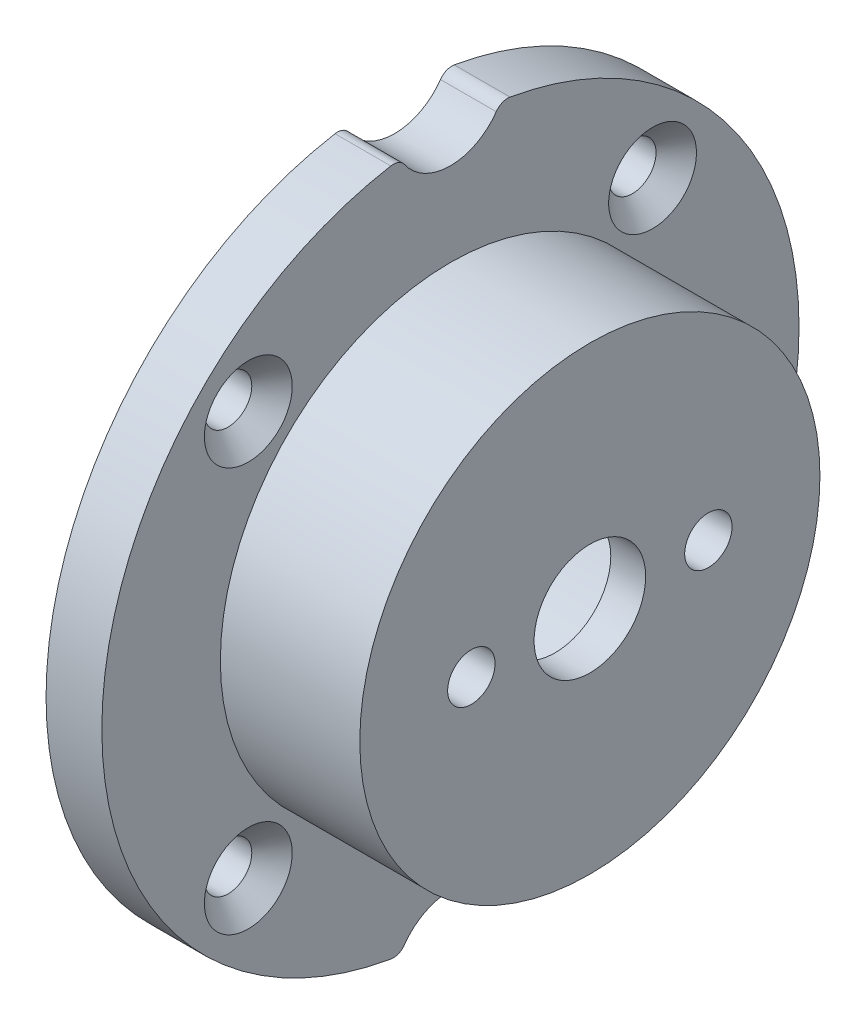
SolidWorks part; units mm, degrees
material "ABS"
ref_plane "Front Plane" through (0, 0, 0) normal (0, 0, 1) x (1, 0, 0)
ref_plane "Top Plane" through (0, 0, 0) normal (0, 1, 0) x (1, 0, 0)
ref_plane "Right Plane" through (0, 0, 0) normal (1, 0, 0) x (0, 0, -1)
sketch "Sketch1" plane through (0, 0, 0) normal (1, 0, 0) x (0, 0, -1)
  circle A0 centre (0, 0) radius 25
extrude "Boss-Extrude1" add sketch "Sketch1" along normal blind 4
sketch "Sketch2" plane through (4, 0, 0) normal (1, 0, 0) x (0, 0, -1)
  circle A0 centre (0, 0) radius 16.5
extrude "Boss-Extrude2" add sketch "Sketch2" along normal blind 10
sketch "Sketch3" plane through (0, 0, 0) normal (-1, 0, 0) x (0, 0, 1)
  circle A0 centre (0, 0) radius 12.5
extrude "Cut-Extrude1" cut sketch "Sketch3" against normal offset from surface (11.5 mm away) 2.5 up to face at (14, 0, -16.5)
sketch "Sketch4" plane through (14, 0, 0) normal (1, 0, 0) x (0, 0, -1)
  circle A0 centre (0, 0) radius 4
extrude "Cut-Extrude2" cut sketch "Sketch4" against normal blind 4
hole_wizard "M3 Clearance Hole1" positions "Sketch6" profile "Sketch5" hole size "M3" standard "ANSI Metric"
sketch "Sketch6" plane through (14, 0, 0) normal (1, 0, 0) x (0, 0, -1)
  point P0 (8.5, 0)
  point P2 (-8.5, 0)
  dimension "D1" = 8.5
  dimension "D2" = 8.5
sketch "Sketch5" plane through (14, 0, -8.5) normal (0, 1, 0) x (0, 0, -1)
  line L0 (0, 0) -> (0, 10)
  line L1 (0, 10) -> (1.7, 10)
  line L2 (1.7, 10) -> (1.7, 0)
  line L5 (1.7, 0) -> (0, 0)
  line L10 (0, 10) -> (-1.7, 10) construction
  line L11 (0, -6.35) -> (0, 107.95) construction
  dimension "Hole Dia." = 3.4
  dimension "Hole Depth" = 10
  dimension "Drill Angle" = 180
sketch "Sketch7" plane through (4, 0, 0) normal (1, 0, 0) x (0, 0, -1)
  line L0 (0, 0) -> (-14.4957, -14.4957) construction
hole_wizard "CSK for M3 Flat Head Machine Screw1" positions "Sketch9" profile "Sketch8" countersink size "M3" standard "ANSI Metric" end condition through all
sketch "Sketch9" plane through (4, 0, 0) normal (1, 0, 0) x (0, 0, -1)
  point P0 (-14.4957, -14.4957)
sketch "Sketch8" plane through (4, -14.4957, 14.4957) normal (0, 1, 0) x (0, 0, -1)
  line L0 (0, 0) -> (0, 4)
  line L1 (0, 4) -> (1.7, 4)
  line L2 (1.7, 4) -> (1.7, 1.45)
  line L3 (1.7, 1.45) -> (3.15, 0)
  line L5 (3.15, 0) -> (0, 0)
  line L6 (-1.7, 1.45) -> (-3.15, 0) construction
  line L11 (0, -6.35) -> (0, 107.95) construction
  dimension "Thru Hole Dia." = 3.4
  dimension "Thru Hole Depth" = 4
  dimension "Near C'Sink Dia." = 6.3
  dimension "Near C'Sink Angle" = 90
pattern_circular "CirPattern1" count 4 over 360 about axis through (0, 0, 0) along (1, 0, 0) of "CSK for M3 Flat Head Machine Screw1"
sketch "Sketch10" plane through (0, 0, 0) normal (-1, 0, 0) x (0, 0, 1)
  circle A0 centre (0, 0) radius 13.125
extrude "Cut-Extrude3" cut sketch "Sketch10" against normal up to surface (11.5 mm away) up to face at (11.5, 0, -10.2)
sketch "Sketch12" plane through (4, 0, 0) normal (1, 0, 0) x (0, 0, -1)
  line L3 (0, 0) -> (25, 0) construction
  line L7 (0, 0) -> (0, 26.5) construction
  circle A1 centre (0, 0) radius 25 construction
  circle A2 centre (0, 26.5) radius 4
  circle A3 centre (0, -26.5) radius 4
extrude "Cut-Extrude4" cut sketch "Sketch12" against normal blind 10
fillet "Fillet1" radius 1 4 edges at (2, -24.7406, -3.5923) (2, -24.7406, 3.5923) (2, 24.7406, 3.5923) (2, 24.7406, -3.5923)
